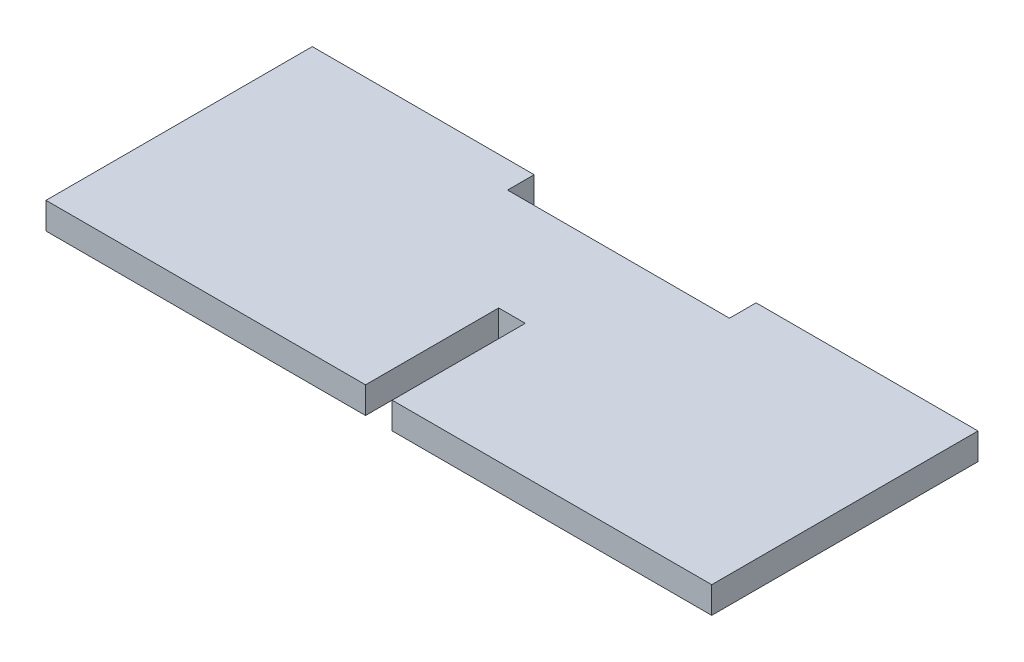
SolidWorks part; units mm, degrees
ref_plane "Plano frontal" through (0, 0, 0) normal (0, 0, 1) x (1, 0, 0)
ref_plane "Plano superior" through (0, 0, 0) normal (0, 1, 0) x (1, 0, 0)
ref_plane "Plano direito" through (0, 0, 0) normal (1, 0, 0) x (0, 0, -1)
sketch "Esboço1" plane through (0, 0, 0) normal (0, 1, 0) x (1, 0, 0)
  line L0 (-1.5, -22.6683) -> (-1.5, 7.3317) construction
  line L1 (-39, 7.3317) -> (36, 7.3317)
  line L2 (-39, 7.3317) -> (-39, -22.6683)
  line L3 (-39, -22.6683) -> (36, -22.6683)
  line L4 (36, 7.3317) -> (36, -22.6683)
  line L5 (-3, -22.6683) -> (-3, -7.6683)
  line L6 (-3, -7.6683) -> (0, -7.6683)
  line L7 (0, -7.6683) -> (0, -22.6683)
  point P11 (-1.5, -7.6683)
  dimension "D1" = 75
  dimension "D2" = 30
  dimension "D3" = 3
  dimension "D4" = 15
  dimension "D5" = 1.5
extrude "Ressalto-extrusão1" add sketch "Esboço1" along normal blind 3 contours L0 L3 L4 L1 | L3 L0 L1 L2 L5 L6 L7
sketch "Esboço2" plane through (0, 0, -7.3317) normal (0, 0, -1) x (-1, 0, 0)
  line L0 (-36, 3) -> (-36, 0) construction
  line L1 (-11, 6.6925) -> (14, 6.6925)
  line L2 (-11, 6.6925) -> (-11, -6.0749)
  line L3 (-11, -6.0749) -> (14, -6.0749)
  line L4 (14, 6.6925) -> (14, -6.0749)
  dimension "D1" = 25
  dimension "D2" = 25
extrude "Corte-extrusão1" cut sketch "Esboço2" against normal blind 3
